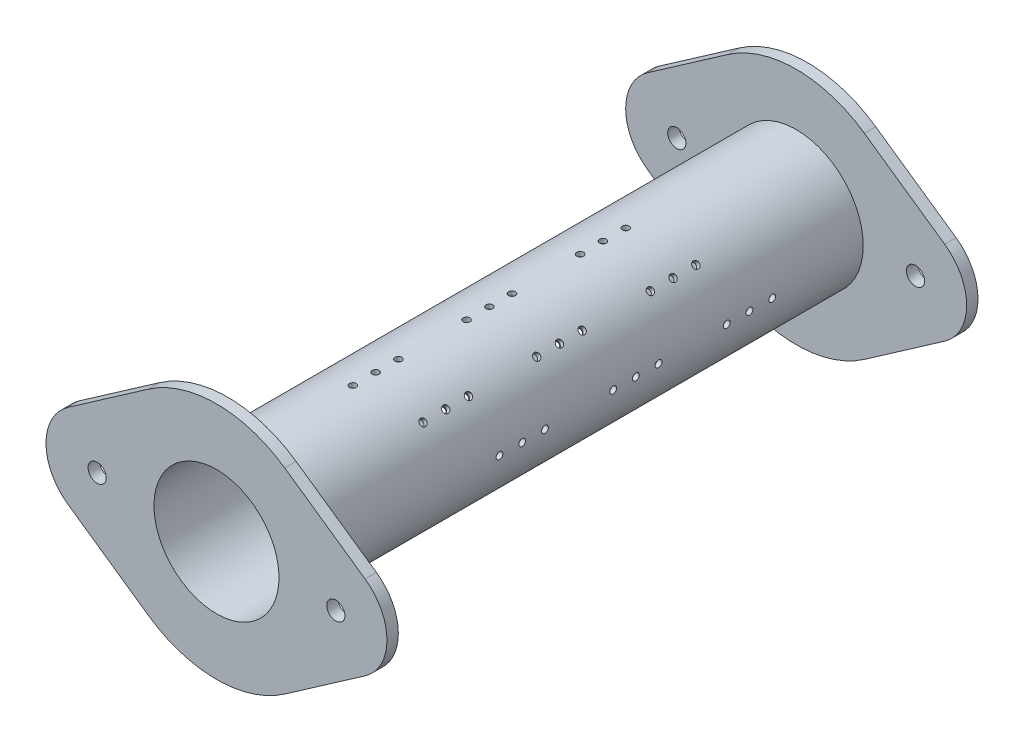
SolidWorks part; units mm, degrees
ref_plane "Front Plane" through (0, 0, 0) normal (0, 0, 1) x (1, 0, 0)
ref_plane "Top Plane" through (0, 0, 0) normal (0, 1, 0) x (1, 0, 0)
ref_plane "Right Plane" through (0, 0, 0) normal (1, 0, 0) x (0, 0, -1)
sketch "Sketch1" plane through (0, 0, 0) normal (0, 0, 1) x (1, 0, 0)
  circle A0 centre (0, 0) radius 27.5
  circle A1 centre (0, 0) radius 29.5
  dimension "D1" = 55
  dimension "D2" = 59
extrude "Boss-Extrude1" add sketch "Sketch1" along normal mid plane 250
sketch "Sketch2" plane through (0, 0, 0) normal (0, 1, 0) x (1, 0, 0)
  line L0 (0, -70) -> (0, -50) construction
  line L1 (-29.5, -125) -> (29.5, -125) construction
  circle A0 centre (0, -70) radius 1.5
  circle A1 centre (0, -60) radius 1.5
  circle A2 centre (0, -50) radius 1.5
  point P6 (0, -35.8778)
  point P10 (0, -60)
  point P11 (0, 0)
  dimension "D1" = 3
  dimension "D2" = 10
  dimension "D3" = 10
  dimension "D4" = 55
extrude "Cut-Extrude1" cut sketch "Sketch2" against normal through all both and the other way through all
sketch "Sketch3" plane through (0, 0, 0) normal (1, 0, 0) x (0, 0, -1)
  line L0 (-125, 0) -> (125, 0) construction
  line L1 (-125, 29.5) -> (-125, -29.5) construction
  line L2 (0, 0) -> (50000, 0) construction
  circle A0 centre (-35, 0) radius 1.5
  circle A1 centre (-25, 0) radius 1.5
  circle A2 centre (-15, 0) radius 1.5
  point P13 (0, 0)
  dimension "D4" = 3
  dimension "D1" = 10
  dimension "D2" = 10
  dimension "D3" = 90
extrude "Cut-Extrude2" cut sketch "Sketch3" against normal through all both and the other way through all
ref_plane "Plane1" through (0, 0, 0) normal (0.7071, 0.7071, 0) x (0, 0, -1)
sketch "Sketch6" plane through (0, 0, 0) normal (0.7071, 0.7071, 0) x (0, 0, -1)
  line L0 (0, 0) -> (-50000, 0) construction
  line L2 (-125, 29.5) -> (-125, -29.5) construction
  circle A0 centre (-40, 0) radius 1.5
  circle A1 centre (-50, 0) radius 1.5
  circle A2 centre (-60, 0) radius 1.5
  point P11 (0, 0)
  dimension "D4" = 3
  dimension "D1" = 10
  dimension "D2" = 10
  dimension "D3" = 65
extrude "Cut-Extrude3" cut sketch "Sketch6" against normal through all both and the other way through all
ref_plane "Plane2" through (0, 0, 0) normal (0.7071, -0.7071, 0) x (0, 0, -1)
sketch "Sketch7" plane through (0, 0, 0) normal (0.7071, -0.7071, 0) x (0, 0, -1)
  line L0 (-125, 0) -> (125, 0) construction
  line L1 (125, -29.5) -> (125, 29.5) construction
  circle A0 centre (60, 0) radius 1.5
  circle A1 centre (50, 0) radius 1.5
  circle A2 centre (40, 0) radius 1.5
  point P10 (0, 0)
  dimension "D1" = 10
  dimension "D2" = 10
  dimension "D4" = 3
  dimension "D3" = 65
extrude "Cut-Extrude4" cut sketch "Sketch7" against normal through all both and the other way through all
pattern_linear "LPattern1" count 3 spacing 50 along (0, 0, -1) of "Cut-Extrude1", "Cut-Extrude3", "Cut-Extrude2"
pattern_linear "LPattern2" count 3 spacing 50 along (0, 0, 1) of "Cut-Extrude4"
sketch "Sketch8" plane through (0, 0, -125) normal (0, 0, -1) x (-1, 0, 0)
  line L0 (30, 43.0842) -> (65.3571, 18.4647)
  line L1 (65.3571, -18.4647) -> (30, -43.0842)
  line L2 (-65.3571, 18.4647) -> (-30, 43.0842)
  line L3 (-65.3571, -18.4647) -> (-30, -43.0842)
  circle A0 centre (0, 0) radius 27.5 construction
  circle A1 centre (0, 0) radius 27.5
  arc A2 (-30, -43.0842) -> (30, -43.0842) centre (0, 0) ccw
  arc A3 (65.3571, -18.4647) -> (65.3571, 18.4647) centre (52.5, 0) ccw
  arc A4 (-65.3571, 18.4647) -> (-65.3571, -18.4647) centre (-52.5, 0) ccw
  arc A5 (30, 43.0842) -> (-30, 43.0842) centre (0, 0) ccw
  circle A6 centre (-52.5, 0) radius 4
  circle A7 centre (52.5, 0) radius 4
  dimension "D1" = 105
  dimension "D2" = 45
  dimension "D3" = 8
  dimension "D4" = 8
extrude "Boss-Extrude2" add sketch "Sketch8" along normal blind 5
mirror "Mirror1" about plane through (0, 0, 0) normal (0, 0, 1) of "Boss-Extrude2"
